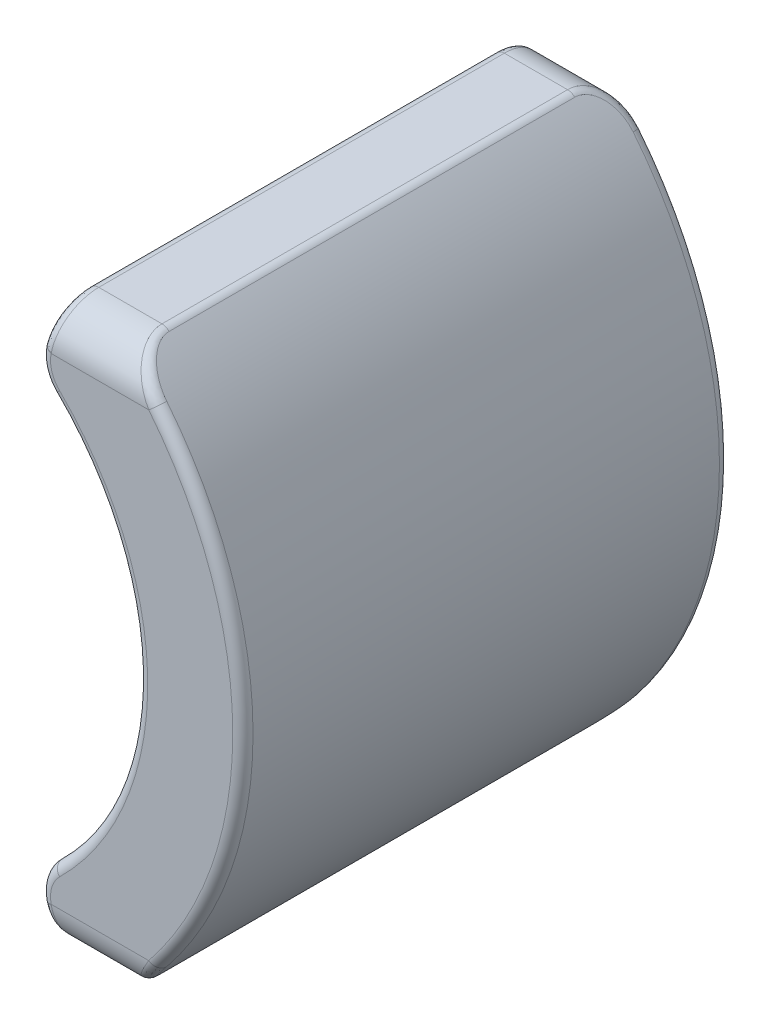
SolidWorks part; units mm, degrees
material "Alnico5"
ref_plane "Front Plane" through (0, 0, 0) normal (0, 0, 1) x (1, 0, 0)
ref_plane "Top Plane" through (0, 0, 0) normal (0, 1, 0) x (1, 0, 0)
ref_plane "Right Plane" through (0, 0, 0) normal (1, 0, 0) x (0, 0, -1)
sketch "Sketch1" plane through (0, 0, 0) normal (0, 0, 1) x (1, 0, 0)
  line L0 (0, 0) -> (9.63, 0) construction
  line L1 (6.7381, -6.88) -> (4.8781, -6.88)
  line L2 (4.8781, -6.88) -> (4.5318, -5.38)
  line L3 (6.7381, 6.88) -> (4.8781, 6.88)
  line L4 (4.8781, 6.88) -> (4.5318, 5.38)
  arc A0 (6.7381, 6.88) -> (6.7381, -6.88) centre (0, 0) cw
  arc A1 (4.5318, 5.38) -> (4.5318, -5.38) centre (0, 0) cw
  dimension "D1" = 9.63
  dimension "D2" = 6.88
  dimension "D3" = 103
  dimension "D4" = 1.86
  dimension "D5" = 1.5
extrude "Boss-Extrude1" add sketch "Sketch1" along normal blind 12
fillet "Fillet1" radius 1 2 edges at (4.5318, -5.38, 6) (4.5318, 5.38, 6)
fillet "Fillet2" radius 1 4 edges at (5.8081, -6.88, 0) (5.8081, 6.88, 0) (5.8081, -6.88, 12) (5.8081, 6.88, 12)
fillet "Fillet3" radius 0.25 24 edges at (4.8161, -6.6112, 0.3178) (4.8781, -6.88, 6) (4.8161, -6.6112, 11.6822) (4.6879, -5.4113, 12) (7.0343, 0, 12) (4.6879, 5.4113, 12) (4.8161, 6.6112, 11.6822) (4.8781, 6.88, 6) (4.8161, 6.6112, 0.3178) (6.8685, -6.7498, 0.5066) (6.7381, -6.88, 6) (6.9882, -6.6258, 11.6661) (9.63, 0, 12) (6.8685, 6.7498, 11.4934) (6.7381, 6.88, 6) (6.9882, 6.6258, 0.3339) (4.6879, 5.4113, 0) (7.0343, 0, 0) (4.6879, -5.4113, 0) (9.63, 0, 0)
